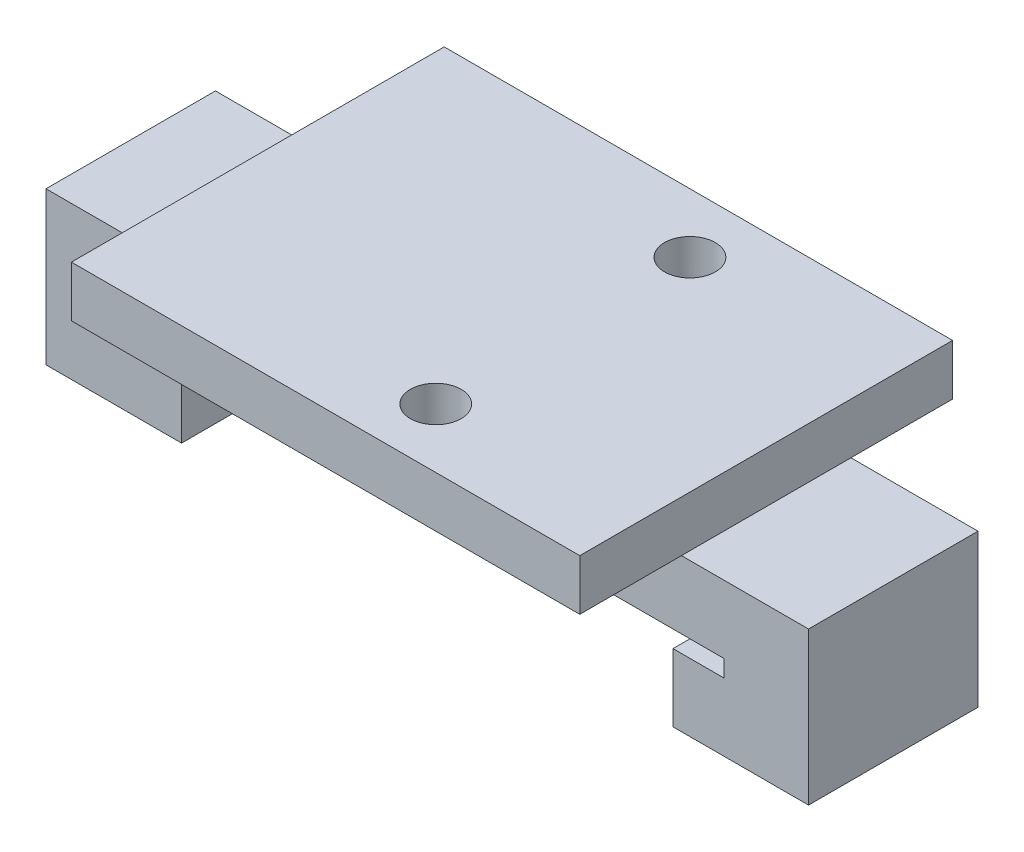
SolidWorks part; units mm, degrees
ref_plane "Płaszczyzna przednia" through (0, 0, 0) normal (0, 0, 1) x (1, 0, 0)
ref_plane "Płaszczyzna górna" through (0, 0, 0) normal (0, 1, 0) x (1, 0, 0)
ref_plane "Płaszczyzna prawa" through (0, 0, 0) normal (1, 0, 0) x (0, 0, -1)
sketch "Sketch2" plane through (0, 0, 0) normal (0, 0, 1) x (1, 0, 0)
  line L0 (0, 0) -> (17.5, 0) construction
  line L5 (0, 0) -> (-17.5, 0) construction
  line L7 (-17.5, 0) -> (-17.5, -1) construction
  line L8 (17.5, 0) -> (17.5, -1) construction
  line L9 (17.5, -1) -> (13.5, -1) construction
  line L10 (13.5, -1) -> (13.5, -7.5) construction
  line L11 (-17.5, -1) -> (-13.5, -1) construction
  line L12 (-13.5, -1) -> (-13.5, -7.5) construction
  line L13 (-13.5, -7.5) -> (13.5, -7.5) construction
  line L14 (-17.5, 0) -> (-17.5, -1) construction
  line L15 (-17.5, 0) -> (-17.5, -1)
  line L16 (-17.5, -1) -> (-14.5, -1)
  line L17 (-14.5, -1) -> (-14.5, -5)
  line L18 (-14.5, -5) -> (-22.5, -5)
  line L19 (-22.5, -5) -> (-22.5, 0)
  line L20 (-22.5, 0) -> (-22.5, 4)
  line L21 (-22.5, 4) -> (22.5, 4)
  line L22 (22.5, 4) -> (22.5, -5)
  line L23 (22.5, -5) -> (14.5, -5)
  line L24 (14.5, -5) -> (14.5, -1)
  line L25 (14.5, -1) -> (17.5, -1)
  line L26 (17.5, -1) -> (17.5, 0)
  line L27 (17.5, 0) -> (-17.5, 0)
  point P10 (-22.5, 0)
  point P11 (-22.5, -5)
  point P12 (-14.5, -5)
  point P13 (-22.5, 0)
  point P14 (-22.5, 4)
  point P16 (-14.5, -1)
  point P17 (-17.5, -1)
  point P18 (-17.5, 0)
  dimension "D1" = 5
  dimension "D2" = 5
  dimension "D3" = 8
  dimension "D4" = 4
  dimension "D5" = 0
  dimension "D6" = 0
  dimension "D7" = 35
  dimension "D8" = 1
  dimension "D9" = 4
  dimension "D10" = 4
  dimension "D11" = 1
  dimension "D12" = 27
  dimension "D13" = 6.5
  dimension "D14" = 6.5
  dimension "D16" = 3
  dimension "D17" = 1
  dimension "D18" = 9
  dimension "D19" = 9
  dimension "D20" = 8
  dimension "D21" = 1
  dimension "D22" = 0
  dimension "D23" = 0
  dimension "D25" = 45
extrude "Boss-Extrude1" add sketch "Sketch2" along normal blind 10
sketch "Sketch3" plane through (0, 4, 0) normal (0, 1, 0) x (1, 0, 0)
  line L0 (22.5, -10) -> (-22.5, -10) construction
  line L1 (-22.5, -10) -> (-22.5, 0) construction
  line L3 (-15, -16) -> (15, -16)
  line L4 (-15, -16) -> (-15, 6)
  line L5 (-15, 6) -> (15, 6)
  line L6 (15, -16) -> (15, 6)
  line L7 (-15, -16) -> (15, 6) construction
  line L8 (-15, 6) -> (15, -16) construction
  point P0 (0, -5)
  point P5 (0, -5)
  dimension "D1" = 5
  dimension "D2" = 22.5
  dimension "D3" = 22
  dimension "D4" = 30
extrude "Boss-Extrude2" add sketch "Sketch3" along normal blind 3
sketch "Sketch4" plane through (0, 7, 0) normal (0, 1, 0) x (1, 0, 0)
  line L0 (15, -16) -> (15, 6) construction
  line L1 (-3, -12.5) -> (3, -12.5) construction
  line L2 (-3, -12.5) -> (-3, 2.5) construction
  line L3 (-3, 2.5) -> (3, 2.5) construction
  line L4 (3, -12.5) -> (3, 2.5) construction
  line L5 (-3, -12.5) -> (3, 2.5) construction
  line L6 (-3, 2.5) -> (3, -12.5) construction
  circle A0 centre (3, 2.5) radius 1.5
  circle A1 centre (3, -12.5) radius 1.5
  point P0 (0, -5)
  dimension "D1" = 15
  dimension "D2" = 12
extrude "Cut-Extrude1" cut sketch "Sketch4" against normal blind 5
